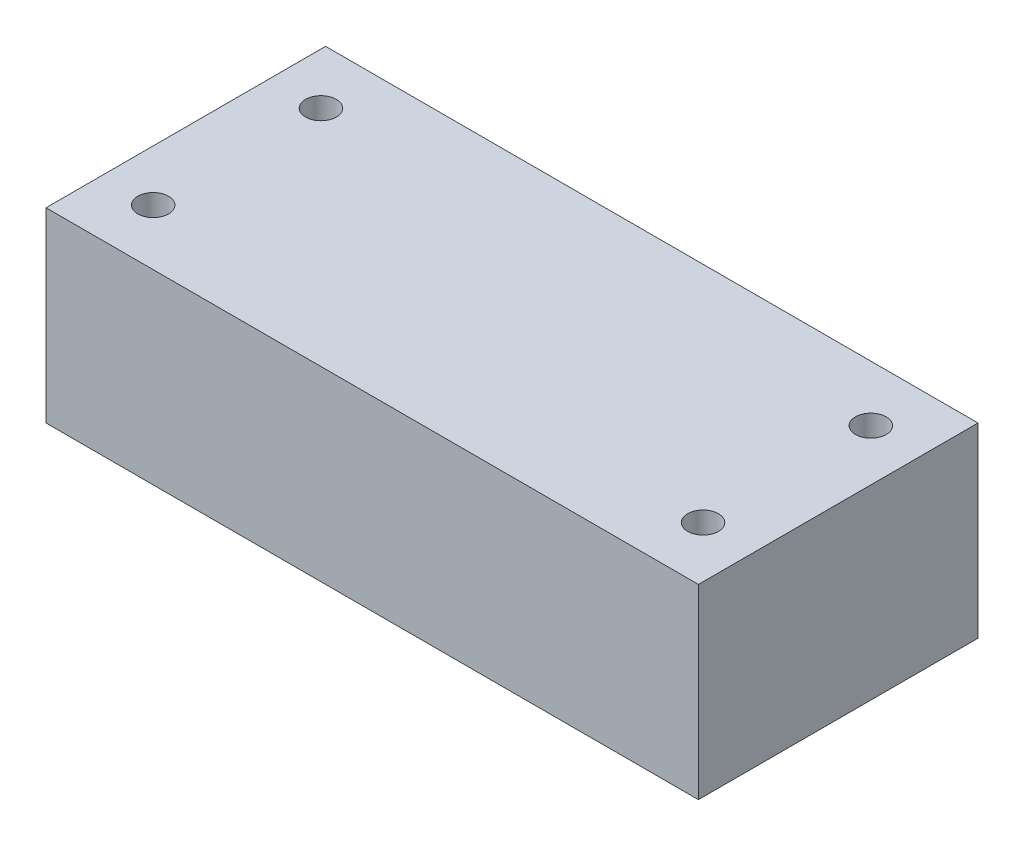
SolidWorks part; units mm, degrees
ref_plane "Front Plane" through (0, 0, 0) normal (0, 0, 1) x (1, 0, 0)
ref_plane "Top Plane" through (0, 0, 0) normal (0, 1, 0) x (1, 0, 0)
ref_plane "Right Plane" through (0, 0, 0) normal (1, 0, 0) x (0, 0, -1)
sketch "Sketch2" plane through (0, 0, 0) normal (0, 1, 0) x (1, 0, 0)
  line L1 (-35, -15) -> (35, -15)
  line L2 (-35, -15) -> (-35, 15)
  line L3 (-35, 15) -> (35, 15)
  line L4 (35, -15) -> (35, 15)
  line L5 (-35, -15) -> (35, 15) construction
  line L6 (-35, 15) -> (35, -15) construction
  point P0 (0, 0)
  dimension "D1" = 70
  dimension "D2" = 30
extrude "Boss-Extrude1" add sketch "Sketch2" along normal blind 20
sketch "Sketch3" plane through (0, 20, 0) normal (0, 1, 0) x (1, 0, 0)
  line L0 (35, -15) -> (35, 15) construction
  line L1 (-29.5, -9) -> (29.5, -9) construction
  line L2 (-29.5, -9) -> (-29.5, 9) construction
  line L3 (-29.5, 9) -> (29.5, 9) construction
  line L4 (29.5, -9) -> (29.5, 9) construction
  line L6 (35, 15) -> (-35, 15) construction
  line L7 (-35, -15) -> (35, -15) construction
  line L8 (-35, 15) -> (-35, -15) construction
  circle A0 centre (-29.5, 9) radius 1.65
  circle A1 centre (29.5, 9) radius 1.65
  circle A2 centre (29.5, -9) radius 1.65
  circle A3 centre (-29.5, -9) radius 1.65
  dimension "D1" = 3.3
  dimension "D2" = 5.5
  dimension "D3" = 6
  dimension "D4" = 6
  dimension "D5" = 5.5
extrude "Cut-Extrude1" cut sketch "Sketch3" against normal blind 30
